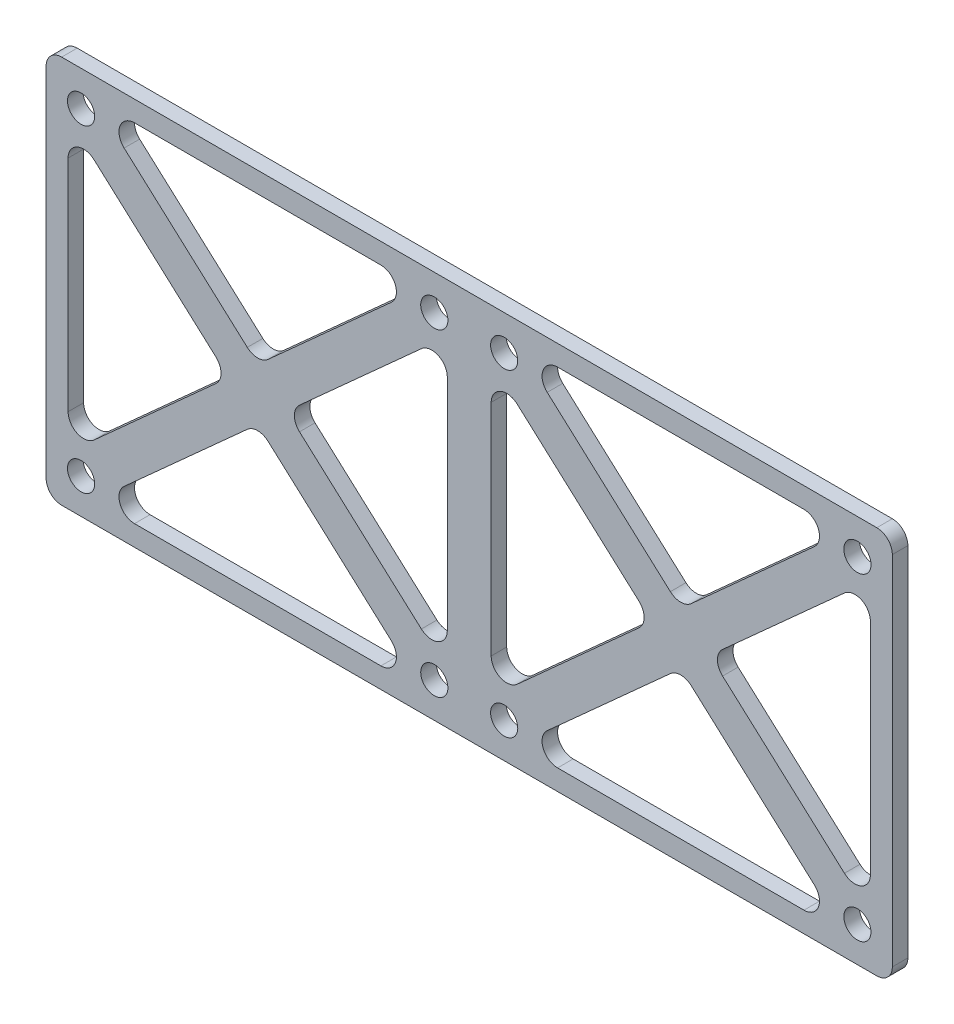
SolidWorks part; units mm, degrees
material "Thornel Mat VMA"
ref_plane "Front Plane" through (0, 0, 0) normal (0, 0, 1) x (1, 0, 0)
ref_plane "Top Plane" through (0, 0, 0) normal (0, 1, 0) x (1, 0, 0)
ref_plane "Right Plane" through (0, 0, 0) normal (1, 0, 0) x (0, 0, -1)
sketch "Sketch1" plane through (0, 0, 0) normal (0, 0, 1) x (1, 0, 0)
  line L0 (0, -25) -> (0, 25) construction
  line L1 (0, 0) -> (-54.5, 0) construction
  line L2 (-51.6735, 18.6428) -> (-30.9846, 0)
  line L3 (-54.5, -25) -> (54.5, -25)
  line L4 (-54.5, -25) -> (-54.5, 25)
  line L5 (-54.5, 25) -> (54.5, 25)
  line L6 (54.5, -25) -> (54.5, 25)
  line L7 (-54.5, -25) -> (54.5, 25) construction
  line L8 (-54.5, 25) -> (54.5, -25) construction
  line L9 (-50, 20.5) -> (-4.5, 20.5) construction
  line L10 (-50, 20.5) -> (-50, -20.5) construction
  line L11 (-50, -20.5) -> (-4.5, -20.5) construction
  line L12 (-4.5, 20.5) -> (-4.5, -20.5) construction
  line L13 (-50, 20.5) -> (-4.5, -20.5) construction
  line L14 (-50, -20.5) -> (-4.5, 20.5) construction
  line L15 (-48.3265, -22.3572) -> (-2.8265, 18.6428) construction
  line L16 (-48.3265, 22.3572) -> (-27.25, 3.3652)
  line L17 (-51.6735, -18.6428) -> (-6.1735, 22.3572) construction
  line L18 (-51.6735, 18.6428) -> (-51.6735, -18.6428)
  line L19 (-48.3265, 22.3572) -> (-6.1735, 22.3572)
  line L20 (-2.8265, 18.6428) -> (-2.8265, -18.6428)
  line L21 (-6.1735, -22.3572) -> (-48.3265, -22.3572)
  line L22 (-23.5154, 0) -> (-2.8265, -18.6428)
  line L23 (-48.3265, 22.3572) -> (-2.8265, -18.6428) construction
  line L24 (-27.25, -3.3652) -> (-6.1735, -22.3572)
  line L25 (-51.6735, 18.6428) -> (-6.1735, -22.3572) construction
  line L26 (-23.5154, 0) -> (-2.8265, 18.6428)
  line L27 (-6.1735, 22.3572) -> (-27.25, 3.3652)
  line L28 (-51.6735, -18.6428) -> (-30.9846, 0)
  line L29 (-48.3265, -22.3572) -> (-27.25, -3.3652)
  line L30 (6.1735, -22.3572) -> (48.3265, -22.3572)
  line L31 (27.25, -3.3652) -> (6.1735, -22.3572)
  line L32 (48.3265, -22.3572) -> (27.25, -3.3652)
  line L33 (51.6735, 18.6428) -> (51.6735, -18.6428)
  line L34 (51.6735, 18.6428) -> (30.9846, 0)
  line L35 (51.6735, -18.6428) -> (30.9846, 0)
  line L36 (48.3265, 22.3572) -> (6.1735, 22.3572)
  line L37 (48.3265, 22.3572) -> (27.25, 3.3652)
  line L38 (6.1735, 22.3572) -> (27.25, 3.3652)
  line L39 (23.5154, 0) -> (2.8265, -18.6428)
  line L40 (2.8265, 18.6428) -> (2.8265, -18.6428)
  line L41 (23.5154, 0) -> (2.8265, 18.6428)
  circle A0 centre (-4.5, 20.5) radius 1.75
  circle A1 centre (-4.5, -20.5) radius 1.75
  circle A2 centre (-50, 20.5) radius 1.75
  circle A3 centre (-50, -20.5) radius 1.75
  circle A4 centre (50, -20.5) radius 1.75
  circle A5 centre (4.5, -20.5) radius 1.75
  circle A6 centre (4.5, 20.5) radius 1.75
  circle A7 centre (50, 20.5) radius 1.75
  point P3 (-27.25, 0)
  point P4 (0, 0)
  dimension "D3" = 3.5
  dimension "D6" = 45.5
  dimension "D1" = 50
  dimension "D2" = 4.5
  dimension "D4" = 4.5
  dimension "D7" = 4.5
  dimension "D5" = 45.5
  dimension "D8" = 2.5
extrude "Boss-Extrude1" add sketch "Sketch1" along normal blind 2
fillet "Fillet1" radius 2 28 edges at (54.5, -25, 1) (54.5, 25, 1) (-54.5, -25, 1) (-54.5, 25, 1) (2.8265, 18.6428, 1) (2.8265, -18.6428, 1) (23.5154, 0, 1) (30.9846, 0, 1) (51.6735, -18.6428, 1) (51.6735, 18.6428, 1) (-23.5154, 0, 1) (-2.8265, -18.6428, 1) (-2.8265, 18.6428, 1) (-51.6735, -18.6428, 1) (-30.9846, 0, 1) (-6.1735, 22.3572, 1) (-27.25, 3.3652, 1) (-27.25, -3.3652, 1) (-48.3265, -22.3572, 1) (-6.1735, -22.3572, 1) (6.1735, -22.3572, 1) (48.3265, -22.3572, 1) (27.25, -3.3652, 1) (48.3265, 22.3572, 1) (6.1735, 22.3572, 1) (27.25, 3.3652, 1) (-51.6735, 18.6428, 1) (-48.3265, 22.3572, 1)
